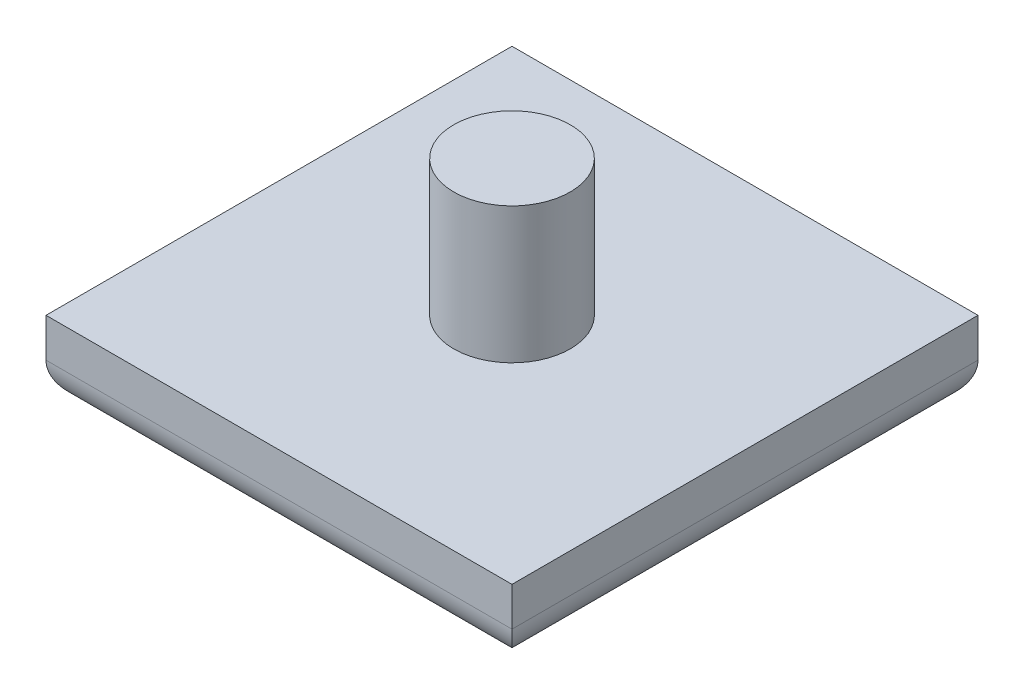
SolidWorks part; units mm, degrees
ref_plane "Front Plane" through (0, 0, 0) normal (0, 0, 1) x (1, 0, 0)
ref_plane "Top Plane" through (0, 0, 0) normal (0, 1, 0) x (1, 0, 0)
ref_plane "Right Plane" through (0, 0, 0) normal (1, 0, 0) x (0, 0, -1)
sketch "Sketch1" plane through (0, 0, 0) normal (0, 1, 0) x (1, 0, 0)
  line L1 (-15.24, 15.24) -> (15.24, 15.24)
  line L2 (-15.24, 15.24) -> (-15.24, -15.24)
  line L3 (-15.24, -15.24) -> (15.24, -15.24)
  line L4 (15.24, 15.24) -> (15.24, -15.24)
  line L5 (-15.24, 15.24) -> (15.24, -15.24) construction
  line L6 (-15.24, -15.24) -> (15.24, 15.24) construction
  point P0 (0, 0)
  dimension "D1" = 30.48
extrude "Boss-Extrude1" add sketch "Sketch1" along normal blind 5.08
sketch "Sketch2" plane through (0, 5.08, 0) normal (0, 1, 0) x (1, 0, 0)
  circle A0 centre (0, 0) radius 3.81
  dimension "D1" = 7.62
extrude "Boss-Extrude2" add sketch "Sketch2" along normal blind 8.89
fillet "Fillet1" radius 2.54 4 edges at (0, 0, -15.24) (-15.24, 0, 0) (0, 0, 15.24) (15.24, 0, 0)
sketch "Sketch3" plane through (0, 0, 0) normal (0, -1, 0) x (1, 0, 0)
  circle A0 centre (0, 0) radius 2.54
  dimension "D1" = 5.08
extrude "Cut-Extrude1" cut sketch "Sketch3" against normal blind 12.7
